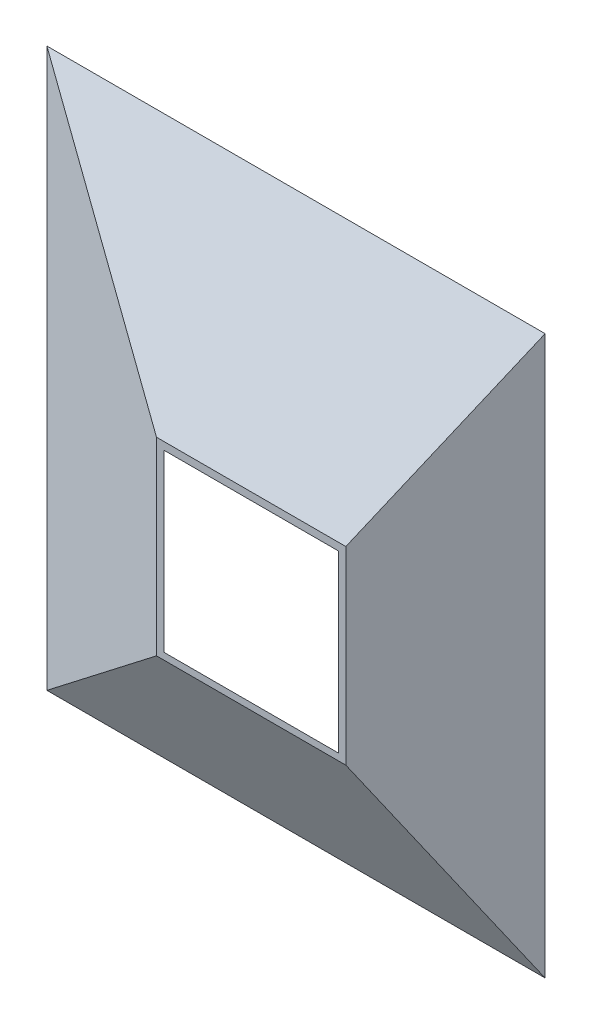
SolidWorks part; units mm, degrees
material "Balsa"
ref_plane "Front Plane" through (0, 0, 0) normal (0, 0, 1) x (1, 0, 0)
ref_plane "Top Plane" through (0, 0, 0) normal (0, 1, 0) x (1, 0, 0)
ref_plane "Right Plane" through (0, 0, 0) normal (1, 0, 0) x (0, 0, -1)
sketch "Sketch1" plane through (0, 0, 0) normal (0, 0, 1) x (1, 0, 0)
  line L1 (-250, -280) -> (250, -280)
  line L2 (-250, -280) -> (-250, 280)
  line L3 (-250, 280) -> (250, 280)
  line L4 (250, -280) -> (250, 280)
  line L5 (-250, -280) -> (250, 280) construction
  line L6 (-250, 280) -> (250, -280) construction
  point P0 (0, 0)
  dimension "D1" = 500
  dimension "D2" = 560
extrude "Boss-Extrude1" add sketch "Sketch1" along normal blind 100
sketch "Sketch2" plane through (0, 280, 0) normal (0, 1, 0) x (1, 0, 0)
  line L0 (250, -100) -> (150, -100)
  line L1 (250, -100) -> (-250, -100) construction
  line L2 (150, -100) -> (250, 0)
  line L3 (250, 0) -> (250, -100)
extrude "Cut-Extrude2" cut sketch "Sketch2" against normal blind 560
sketch "Sketch3" plane through (0, 280, 0) normal (0, 1, 0) x (1, 0, 0)
  line L1 (150, -100) -> (-250, -100) construction
  line L2 (-50, -100) -> (-250, 0)
  line L3 (-250, 0) -> (-250, -100)
  line L4 (-250, -100) -> (-50, -100)
sketch "Sketch6" plane through (-250, 0, 0) normal (-1, 0, 0) x (0, 0, 1)
  line L2 (100, 280) -> (100, -280) construction
  line L4 (100, 95) -> (0, 280)
  line L5 (0, 280) -> (100, 280)
  line L6 (0, 280) -> (100, 280) construction
  line L7 (100, 280) -> (100, 95)
  line L8 (100, -95) -> (0, -280)
  line L9 (0, -280) -> (100, -280)
  line L10 (100, -280) -> (100, -95)
extrude "Cut-Extrude4" cut sketch "Sketch6" against normal blind 560
sketch "Sketch7" plane through (0, 0, 0) normal (0, 1, 0) x (1, 0, 0)
  line L0 (-250, 0) -> (-250, -100)
  line L1 (-250, -100) -> (-40, -100)
  line L2 (150, -100) -> (-250, -100) construction
  line L3 (-40, -100) -> (-250, 0)
extrude "Cut-Extrude5" cut sketch "Sketch7" along normal through all both and the other way through all
sketch "Sketch8" plane through (0, 0, 100) normal (0, 0, 1) x (1, 0, 0)
  line L1 (142.4413, 87.4212) -> (-32.4199, 87.4212)
  line L2 (142.4413, 87.4212) -> (142.4413, -88.1825)
  line L3 (142.4413, -88.1825) -> (-32.4199, -88.1825)
  line L4 (-32.4199, 87.4212) -> (-32.4199, -88.1825)
sketch "Sketch9" plane through (0, 0, 0) normal (0, 0, -1) x (-1, 0, 0)
  line L1 (235.2982, 269.6603) -> (-241.1888, 269.6603)
  line L2 (235.2982, 269.6603) -> (235.2982, -264.4241)
  line L3 (235.2982, -264.4241) -> (-241.1888, -264.4241)
  line L4 (-241.1888, 269.6603) -> (-241.1888, -264.4241)
loft "Cut-Loft1" cut profiles "Sketch9", "Sketch8"
